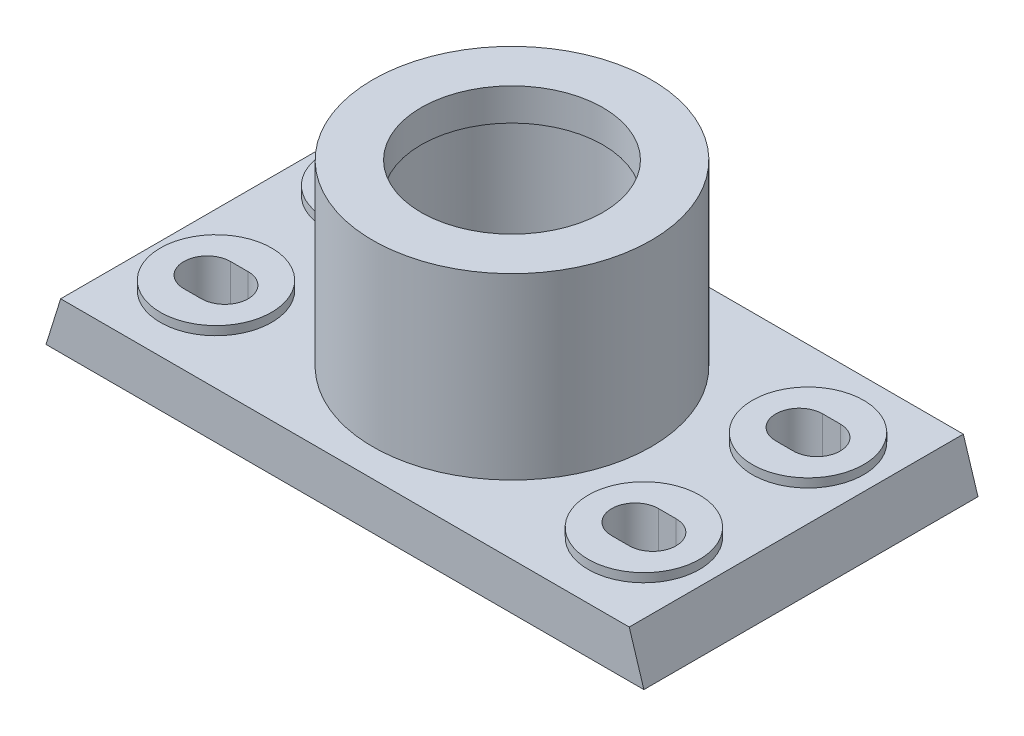
SolidWorks part; units mm, degrees
ref_plane "Front Plane" through (0, 0, 0) normal (0, 0, 1) x (1, 0, 0)
ref_plane "Top Plane" through (0, 0, 0) normal (0, 1, 0) x (1, 0, 0)
ref_plane "Right Plane" through (0, 0, 0) normal (1, 0, 0) x (0, 0, -1)
sketch "Sketch2" plane through (0, 0, 0) normal (0, 0, 1) x (1, 0, 0)
  line L0 (-145.7619, 0) -> (157.5205, 0) construction
  line L1 (0, 106.3818) -> (0, -101.0572) construction
  line L2 (-102, 0) -> (-97, 16)
  line L3 (-97, 16) -> (97, 16)
  line L4 (102, 0) -> (97, 16)
  line L5 (-102, 0) -> (102, 0)
  point P10 (0, 16)
  dimension "D1" = 204
  dimension "D2" = 16
  dimension "D3" = 5
extrude "Boss-Extrude1" add sketch "Sketch2" against normal blind 114
sketch "Sketch3" plane through (0, 0, 0) normal (0, -1, 0) x (1, 0, 0)
  line L0 (0, 26.2438) -> (0, -128.9097)
  line L1 (92, -104) -> (9.5, -104)
  line L2 (-92, -10) -> (-9.5, -10)
  line L3 (-92, -10) -> (-92, -104)
  line L4 (-92, -104) -> (-9.5, -104)
  line L5 (-9.5, -10) -> (-9.5, -104)
  line L6 (-92, -10) -> (-9.5, -104) construction
  line L7 (-92, -104) -> (-9.5, -10) construction
  line L8 (9.5, -10) -> (9.5, -104)
  line L9 (92, -10) -> (92, -104)
  line L10 (92, -10) -> (9.5, -10)
  point P2 (-50.75, -57)
  dimension "D1" = 82.5
  dimension "D2" = 10
  dimension "D3" = 47
  dimension "D4" = 57
  dimension "D5" = 9.5
extrude "Cut-Extrude1" cut sketch "Sketch3" against normal blind 3 contours L5 L2 L3 L4 | L9 L10 L8 L1
sketch "Sketch4" plane through (0, 16, 0) normal (0, 1, 0) x (1, 0, 0)
  line L0 (-76, 85) -> (-70, 85) construction
  line L1 (-76, 93) -> (-70, 93)
  line L2 (-76, 77) -> (-70, 77)
  line L3 (-102, 114) -> (-102, 0) construction
  line L4 (0, 0) -> (0, 136.1768)
  line L5 (-102, 57) -> (112.7959, 57)
  line L6 (76, 85) -> (70, 85) construction
  line L7 (76, 93) -> (70, 93)
  line L8 (76, 77) -> (70, 77)
  line L9 (76, 29) -> (70, 29) construction
  line L10 (76, 21) -> (70, 21)
  line L11 (76, 37) -> (70, 37)
  line L12 (-76, 29) -> (-70, 29) construction
  line L13 (-76, 21) -> (-70, 21)
  line L14 (-76, 37) -> (-70, 37)
  arc A0 (-76, 93) -> (-76, 77) centre (-76, 85) ccw
  arc A1 (-70, 77) -> (-70, 93) centre (-70, 85) ccw
  arc A2 (76, 93) -> (76, 77) centre (76, 85) cw
  arc A3 (70, 77) -> (70, 93) centre (70, 85) cw
  arc A4 (76, 21) -> (76, 37) centre (76, 29) ccw
  arc A5 (70, 37) -> (70, 21) centre (70, 29) ccw
  arc A6 (-76, 21) -> (-76, 37) centre (-76, 29) cw
  arc A7 (-70, 37) -> (-70, 21) centre (-70, 29) cw
  point P2 (-73, 85)
  point P7 (-102, 57)
  point P19 (73, 85)
  point P26 (73, 29)
  point P33 (-73, 29)
  dimension "D3" = 29
  dimension "D1" = 16
  dimension "D2" = 22
  dimension "D4" = 28
extrude "Cut-Extrude2" cut sketch "Sketch4" against normal through all contours L2 A1 L1 A0 | A3 L8 A2 L7 | A7 L14 A6 L13 | L11 A5 L10 A4
sketch "Sketch5" plane through (0, 16, 0) normal (0, 1, 0) x (1, 0, 0)
  line L0 (-102, 114) -> (-102, 0) construction
  line L1 (-102, 57) -> (135.4992, 57)
  line L2 (0, 0) -> (0, 134.5697)
  circle A0 centre (-73, 85) radius 19
  circle A1 centre (73, 85) radius 19
  circle A2 centre (-73, 29) radius 19
  circle A3 centre (73, 29) radius 19
  point P2 (-102, 57)
  line M1 (70, 37) -> (76, 37)
  arc M2 (76, 37) -> (76, 21) centre (76, 29) cw
  line M3 (76, 21) -> (70, 21)
  arc M4 (70, 21) -> (70, 37) centre (70, 29) cw
  line M5 (76, 77) -> (70, 77)
  arc M6 (70, 77) -> (70, 93) centre (70, 85) cw
  line M7 (70, 93) -> (76, 93)
  arc M8 (76, 93) -> (76, 77) centre (76, 85) cw
  line M9 (-70, 77) -> (-76, 77)
  arc M10 (-76, 77) -> (-76, 93) centre (-76, 85) cw
  line M11 (-76, 93) -> (-70, 93)
  arc M12 (-70, 93) -> (-70, 77) centre (-70, 85) cw
  line M17 (-76, 37) -> (-70, 37)
  arc M18 (-70, 37) -> (-70, 21) centre (-70, 29) cw
  line M19 (-70, 21) -> (-76, 21)
  arc M20 (-76, 21) -> (-76, 37) centre (-76, 29) cw
  dimension "D1" = 38
  dimension "D2" = 29
  dimension "D3" = 28
extrude "Boss-Extrude2" add sketch "Sketch5" along normal blind 3 contours A0 M12 M9 M10 M11 | A1 M8 M5 M6 M7 | A3 M4 M1 M2 M3 | A2 M20 M17 M18 M19
sketch "Sketch6" plane through (0, 16, 0) normal (0, 1, 0) x (1, 0, 0)
  circle A0 centre (0, 57) radius 31
  circle A1 centre (0, 57) radius 47.5
  dimension "D1" = 62
  dimension "D2" = 95
  dimension "D3" = 57
  dimension "D4" = 102
extrude "Boss-Extrude4" add sketch "Sketch6" along normal blind 61
ref_plane "Plane1" through (0, 0, -57) normal (0, 0, 1) x (1, 0, 0)
sketch "Sketch8" plane through (0, 0, -57) normal (0, 0, 1) x (1, 0, 0)
  line L0 (47.5, 77) -> (-47.5, 77) construction
  line L1 (-32.5, 66) -> (-29.5, 66)
  line L2 (-32.5, 66) -> (-32.5, 30.455)
  line L3 (-32.5, 30.455) -> (-29.5, 30.455)
  line L4 (-29.5, 66) -> (-29.5, 30.455)
  line L5 (0, 107.1062) -> (0, -5.921) construction
  dimension "D1" = 3
  dimension "D2" = 32.5
  dimension "D3" = 11
revolve "Cut-Revolve1" cut sketch "Sketch8" angle 360 about L5
sketch "Sketch9" plane through (0, 16, 0) normal (0, 1, 0) x (1, 0, 0)
  line L1 (-42.35, 57) -> (42.35, 57) construction
  circle A0 centre (-22, 57) radius 1.5
  dimension "D2" = 3
  dimension "D1" = 22
extrude "Cut-Extrude3" cut sketch "Sketch9" against normal blind 5
